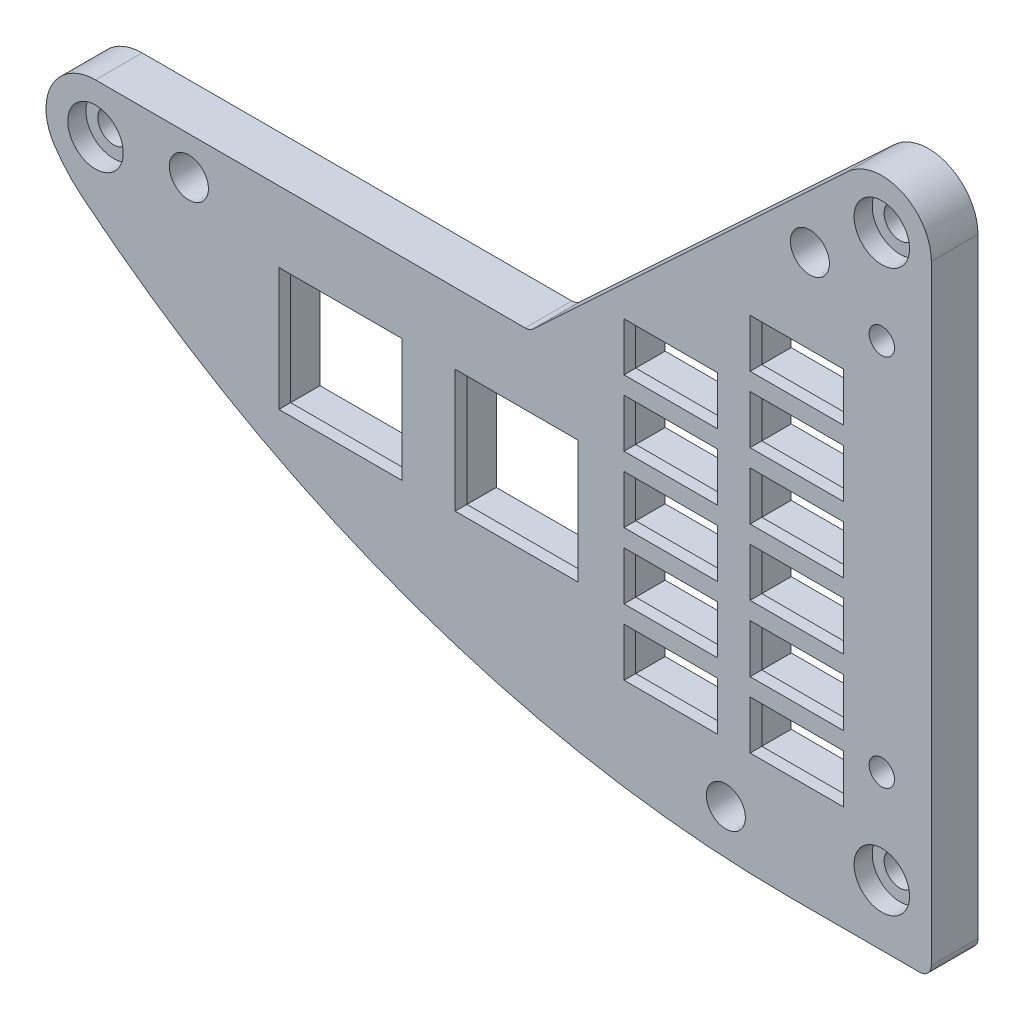
SolidWorks part; units mm, degrees
ref_plane "Front Plane" through (0, 0, 0) normal (0, 0, 1) x (1, 0, 0)
ref_plane "Top Plane" through (0, 0, 0) normal (0, 1, 0) x (1, 0, 0)
ref_plane "Right Plane" through (0, 0, 0) normal (1, 0, 0) x (0, 0, -1)
sketch "Sketch2" plane through (0, 0, -77.851) normal (0, 0, 1) x (1, 0, 0)
  line L0 (-595.8647, 521.6144) -> (-595.8647, 503.8344) construction
  line L1 (-595.8647, 503.8344) -> (-578.0847, 503.8344) construction
  line L2 (-578.0847, 503.8344) -> (-578.0847, 521.6144) construction
  line L3 (-578.0847, 521.6144) -> (-595.8647, 521.6144) construction
  line L4 (-530.5867, 481.6475) -> (-530.5867, 566.1727)
  line L5 (-541.9099, 571.0939) -> (-585.1967, 530.7013)
  line L6 (-585.1967, 530.7013) -> (-644.2517, 530.7013)
  line L7 (-549.6367, 481.6475) -> (-530.5867, 481.6475)
  line L8 (-530.5867, 481.6475) -> (-530.5867, 566.1727)
  line L9 (-541.9099, 571.0939) -> (-585.1967, 530.7013)
  line L10 (-585.1967, 530.7013) -> (-644.2517, 530.7013)
  line L11 (-549.6367, 481.6475) -> (-530.5867, 481.6475)
  line L12 (-572.3697, 495.935) -> (-559.6697, 495.935) construction
  line L13 (-559.6697, 495.935) -> (-559.6697, 502.539) construction
  line L14 (-559.6697, 502.539) -> (-572.3697, 502.539) construction
  line L15 (-572.3697, 502.539) -> (-572.3697, 495.935) construction
  line L16 (-572.3697, 504.9266) -> (-559.6697, 504.9266) construction
  line L17 (-559.6697, 504.9266) -> (-559.6697, 511.5306) construction
  line L18 (-559.6697, 511.5306) -> (-572.3697, 511.5306) construction
  line L19 (-572.3697, 511.5306) -> (-572.3697, 504.9266) construction
  line L20 (-555.2247, 502.539) -> (-555.2247, 495.935) construction
  line L21 (-555.2247, 495.935) -> (-542.5247, 495.935) construction
  line L22 (-542.5247, 495.935) -> (-542.5247, 502.539) construction
  line L23 (-542.5247, 502.539) -> (-555.2247, 502.539) construction
  line L24 (-555.2247, 504.9266) -> (-542.5247, 504.9266) construction
  line L25 (-542.5247, 504.9266) -> (-542.5247, 511.5306) construction
  line L26 (-542.5247, 511.5306) -> (-555.2247, 511.5306) construction
  line L27 (-555.2247, 511.5306) -> (-555.2247, 504.9266) construction
  line L28 (-555.2247, 513.9182) -> (-542.5247, 513.9182) construction
  line L29 (-542.5247, 513.9182) -> (-542.5247, 520.5222) construction
  line L30 (-542.5247, 520.5222) -> (-555.2247, 520.5222) construction
  line L31 (-555.2247, 520.5222) -> (-555.2247, 513.9182) construction
  line L32 (-572.3697, 513.9182) -> (-559.6697, 513.9182) construction
  line L33 (-559.6697, 513.9182) -> (-559.6697, 520.5222) construction
  line L34 (-559.6697, 520.5222) -> (-572.3697, 520.5222) construction
  line L35 (-572.3697, 520.5222) -> (-572.3697, 513.9182) construction
  line L36 (-572.3697, 522.9098) -> (-559.6697, 522.9098) construction
  line L37 (-559.6697, 522.9098) -> (-559.6697, 529.5138) construction
  line L38 (-559.6697, 529.5138) -> (-572.3697, 529.5138) construction
  line L39 (-572.3697, 529.5138) -> (-572.3697, 522.9098) construction
  line L40 (-555.2247, 522.9098) -> (-542.5247, 522.9098) construction
  line L41 (-542.5247, 522.9098) -> (-542.5247, 529.5138) construction
  line L42 (-542.5247, 529.5138) -> (-555.2247, 529.5138) construction
  line L43 (-555.2247, 529.5138) -> (-555.2247, 522.9098) construction
  line L44 (-555.2247, 531.9014) -> (-542.5247, 531.9014) construction
  line L45 (-542.5247, 531.9014) -> (-542.5247, 538.5054) construction
  line L46 (-542.5247, 538.5054) -> (-555.2247, 538.5054) construction
  line L47 (-555.2247, 538.5054) -> (-555.2247, 531.9014) construction
  line L48 (-572.3697, 531.9014) -> (-559.6697, 531.9014) construction
  line L49 (-559.6697, 531.9014) -> (-559.6697, 538.5054) construction
  line L50 (-559.6697, 538.5054) -> (-572.3697, 538.5054) construction
  line L51 (-572.3697, 538.5054) -> (-572.3697, 531.9014) construction
  line L52 (-555.2247, 540.893) -> (-542.5247, 540.893) construction
  line L53 (-542.5247, 540.893) -> (-542.5247, 547.497) construction
  line L54 (-542.5247, 547.497) -> (-555.2247, 547.497) construction
  line L55 (-555.2247, 547.497) -> (-555.2247, 540.893) construction
  line L56 (-555.2247, 513.9182) -> (-542.5247, 513.9182) construction
  line L57 (-595.8647, 521.6144) -> (-595.8647, 503.8344) construction
  line L58 (-595.8647, 503.8344) -> (-578.0847, 503.8344) construction
  line L59 (-578.0847, 503.8344) -> (-578.0847, 521.6144) construction
  line L60 (-578.0847, 521.6144) -> (-595.8647, 521.6144) construction
  line L61 (-572.3697, 495.935) -> (-559.6697, 495.935)
  line L62 (-559.6697, 495.935) -> (-559.6697, 502.539)
  line L63 (-559.6697, 502.539) -> (-572.3697, 502.539)
  line L64 (-572.3697, 502.539) -> (-572.3697, 495.935)
  line L65 (-572.3697, 504.9266) -> (-559.6697, 504.9266)
  line L66 (-559.6697, 504.9266) -> (-559.6697, 511.5306)
  line L67 (-559.6697, 511.5306) -> (-572.3697, 511.5306)
  line L68 (-572.3697, 511.5306) -> (-572.3697, 504.9266)
  line L69 (-555.2247, 502.539) -> (-555.2247, 495.935)
  line L70 (-555.2247, 495.935) -> (-542.5247, 495.935)
  line L71 (-542.5247, 495.935) -> (-542.5247, 502.539)
  line L72 (-542.5247, 502.539) -> (-555.2247, 502.539)
  line L73 (-555.2247, 504.9266) -> (-542.5247, 504.9266)
  line L74 (-542.5247, 504.9266) -> (-542.5247, 511.5306)
  line L75 (-542.5247, 511.5306) -> (-555.2247, 511.5306)
  line L76 (-555.2247, 511.5306) -> (-555.2247, 504.9266)
  line L77 (-555.2247, 513.9182) -> (-542.5247, 513.9182)
  line L78 (-542.5247, 513.9182) -> (-542.5247, 520.5222)
  line L79 (-542.5247, 520.5222) -> (-555.2247, 520.5222)
  line L80 (-555.2247, 520.5222) -> (-555.2247, 513.9182)
  line L81 (-572.3697, 513.9182) -> (-559.6697, 513.9182)
  line L82 (-559.6697, 513.9182) -> (-559.6697, 520.5222)
  line L83 (-559.6697, 520.5222) -> (-572.3697, 520.5222)
  line L84 (-572.3697, 520.5222) -> (-572.3697, 513.9182)
  line L85 (-572.3697, 522.9098) -> (-559.6697, 522.9098)
  line L86 (-559.6697, 522.9098) -> (-559.6697, 529.5138)
  line L87 (-559.6697, 529.5138) -> (-572.3697, 529.5138)
  line L88 (-572.3697, 529.5138) -> (-572.3697, 522.9098)
  line L89 (-555.2247, 522.9098) -> (-542.5247, 522.9098)
  line L90 (-542.5247, 522.9098) -> (-542.5247, 529.5138)
  line L91 (-542.5247, 529.5138) -> (-555.2247, 529.5138)
  line L92 (-555.2247, 529.5138) -> (-555.2247, 522.9098)
  line L93 (-555.2247, 531.9014) -> (-542.5247, 531.9014)
  line L94 (-542.5247, 531.9014) -> (-542.5247, 538.5054)
  line L95 (-542.5247, 538.5054) -> (-555.2247, 538.5054)
  line L96 (-555.2247, 538.5054) -> (-555.2247, 531.9014)
  line L97 (-572.3697, 531.9014) -> (-559.6697, 531.9014)
  line L98 (-559.6697, 531.9014) -> (-559.6697, 538.5054)
  line L99 (-559.6697, 538.5054) -> (-572.3697, 538.5054)
  line L100 (-572.3697, 538.5054) -> (-572.3697, 531.9014)
  line L101 (-555.2247, 540.893) -> (-542.5247, 540.893)
  line L102 (-542.5247, 540.893) -> (-542.5247, 547.497)
  line L103 (-542.5247, 547.497) -> (-555.2247, 547.497)
  line L104 (-555.2247, 547.497) -> (-555.2247, 540.893)
  line L105 (-555.2247, 513.9182) -> (-542.5247, 513.9182)
  line L106 (-578.0847, 503.8344) -> (-595.8647, 521.6144) construction
  line L108 (-578.6181, 521.081) -> (-595.3313, 521.081)
  line L109 (-578.6181, 521.081) -> (-578.6181, 504.3678)
  line L110 (-578.6181, 504.3678) -> (-595.3313, 504.3678)
  line L111 (-595.3313, 521.081) -> (-595.3313, 504.3678)
  line L112 (-578.6181, 521.081) -> (-595.3313, 504.3678) construction
  line L113 (-578.6181, 504.3678) -> (-595.3313, 521.081) construction
  arc A4 (-530.5867, 566.1727) -> (-541.9099, 571.0939) centre (-537.3177, 566.1727) ccw
  arc A5 (-644.2517, 530.7013) -> (-649.8762, 520.2727) centre (-644.2517, 523.9703) ccw
  arc A6 (-649.8762, 520.2727) -> (-646.0191, 515.9958) centre (-634.0129, 530.7013) ccw
  arc A7 (-646.0191, 515.9958) -> (-549.6367, 481.6475) centre (-549.6367, 634.0475) ccw
  arc A8 (-530.5867, 566.1727) -> (-541.9099, 571.0939) centre (-537.3177, 566.1727) ccw
  arc A9 (-644.2517, 530.7013) -> (-649.8762, 520.2727) centre (-644.2517, 523.9703) ccw
  arc A10 (-649.8762, 520.2727) -> (-646.0191, 515.9958) centre (-634.0129, 530.7013) ccw
  arc A11 (-646.0191, 515.9958) -> (-549.6367, 481.6475) centre (-549.6367, 634.0475) ccw
  point P58 (-586.9747, 512.7244)
  dimension "D2" = 16.7132
  dimension "D1" = 0
extrude "Boss-Extrude1" add sketch "Sketch2" against normal blind 6.35 contours A10 A11 L11 L8 A8 L9 L10 A9 L60 L59 L58 L57 L64 L63 L62 L61 L68 L67 L66 L65 L72 L71 L70 L69 L76 L75 L74 L73 L80 L79 L78 L77 L84 L83 L82 L81 L88 L87 L86 L85 L92 L91
hole_wizard "CBORE for #6 Pan Head Machine Screw1" positions "Sketch4" profile "Sketch3" counterbore size "#6" standard "ANSI Inch" end condition through all
sketch "Sketch4" plane through (0, 0, -77.851) normal (0, 0, 1) x (1, 0, 0)
  point P0 (-537.3177, 489.9025)
  point P3 (-537.3177, 566.1727)
  point P6 (-644.2517, 523.9703)
sketch "Sketch3" plane through (-537.3177, 489.9025, -77.851) normal (1, 0, 0) x (0, -1, 0)
  line L0 (0, 0) -> (0, 6.35)
  line L1 (0, 6.35) -> (2.1526, 6.35)
  line L3 (2.1526, 6.35) -> (2.1526, 2.4638)
  line L4 (2.1526, 2.4638) -> (3.7706, 2.4638)
  line L5 (3.7706, 2.4638) -> (3.7706, 0)
  line L7 (3.7706, 0) -> (0, 0)
  line L11 (0, -6.35) -> (0, 107.95) construction
  dimension "Thru Hole Dia." = 4.3053
  dimension "Thru Hole Depth" = 6.35
  dimension "C'Bore Dia." = 7.5413
  dimension "C'Bore Depth" = 2.4638
hole_wizard "#6 Threaded Insert Tapered Hole" positions "Sketch6" profile "Sketch5" legacy
sketch "Sketch6" plane through (0, 0, -77.851) normal (0, 0, 1) x (1, 0, 0)
  point P0 (-558.5267, 487.9975)
  point P3 (-547.0967, 558.9583)
  point P6 (-631.5517, 525.5578)
sketch "Sketch5" plane through (-558.5267, 487.9975, -77.851) normal (1, 0, 0) x (0, -1, 0)
  line L0 (0, 0) -> (0, 3.81)
  line L1 (0, 3.81) -> (2.5273, 3.81)
  line L2 (2.5273, 3.81) -> (2.6543, 0)
  line L3 (2.6543, 0) -> (0, 0)
  line L4 (0, 110) -> (0, -10) construction
  dimension "Minor Diameter" = 5.0546
  dimension "Depth" = 3.81
  dimension "Major Diameter" = 5.3086
sketch "Sketch7" plane through (0, 0, -77.851) normal (0, 0, 1) x (1, 0, 0)
  line L0 (-610.9485, 512.7244) -> (-610.9485, 521.081) construction
  line L2 (-610.9485, 512.7244) -> (-595.3313, 512.7244) construction
  line L3 (-602.5919, 504.3678) -> (-619.3051, 504.3678)
  line L4 (-602.5919, 504.3678) -> (-602.5919, 521.081)
  line L5 (-602.5919, 521.081) -> (-619.3051, 521.081)
  line L6 (-619.3051, 504.3678) -> (-619.3051, 521.081)
  line L7 (-602.5919, 504.3678) -> (-619.3051, 521.081) construction
  line L8 (-602.5919, 521.081) -> (-619.3051, 504.3678) construction
  line L9 (-595.3313, 521.081) -> (-595.3313, 504.3678) construction
  point P5 (-610.9485, 512.7244)
  dimension "D1" = 16.7132
  dimension "D2" = 16.7132
  dimension "D3" = 15.6171
extrude "Cut-Extrude1" cut sketch "Sketch7" against normal through all
sketch "Sketch8" plane through (0, 0, -84.201) normal (0, 0, -1) x (-1, 0, 0)
  line L0 (555.9867, 540.131) -> (555.9867, 548.259)
  line L1 (555.9867, 548.259) -> (541.7627, 548.259)
  line L2 (541.7627, 548.259) -> (541.7627, 540.131)
  line L3 (541.7627, 540.131) -> (555.9867, 540.131)
  line L4 (555.2247, 540.893) -> (555.2247, 547.497)
  line L5 (542.5247, 540.893) -> (555.2247, 540.893)
  line L6 (542.5247, 547.497) -> (542.5247, 540.893)
  line L7 (555.2247, 547.497) -> (542.5247, 547.497)
  line L8 (555.2247, 540.893) -> (555.2247, 547.497) construction
  line L9 (542.5247, 540.893) -> (555.2247, 540.893) construction
  line L10 (542.5247, 547.497) -> (542.5247, 540.893) construction
  line L11 (555.2247, 547.497) -> (542.5247, 547.497) construction
  line L12 (555.2247, 531.9014) -> (555.2247, 538.5054)
  line L13 (542.5247, 531.9014) -> (555.2247, 531.9014)
  line L14 (542.5247, 538.5054) -> (542.5247, 531.9014)
  line L15 (555.2247, 538.5054) -> (542.5247, 538.5054)
  line L16 (555.2247, 531.9014) -> (555.2247, 538.5054) construction
  line L17 (542.5247, 531.9014) -> (555.2247, 531.9014) construction
  line L18 (542.5247, 538.5054) -> (542.5247, 531.9014) construction
  line L19 (555.2247, 538.5054) -> (542.5247, 538.5054) construction
  line L20 (555.2247, 522.9098) -> (555.2247, 529.5138)
  line L21 (542.5247, 522.9098) -> (555.2247, 522.9098)
  line L22 (542.5247, 529.5138) -> (542.5247, 522.9098)
  line L23 (555.2247, 529.5138) -> (542.5247, 529.5138)
  line L24 (555.2247, 522.9098) -> (555.2247, 529.5138) construction
  line L25 (542.5247, 522.9098) -> (555.2247, 522.9098) construction
  line L26 (542.5247, 529.5138) -> (542.5247, 522.9098) construction
  line L27 (555.2247, 529.5138) -> (542.5247, 529.5138) construction
  line L28 (555.2247, 513.9182) -> (555.2247, 520.5222)
  line L29 (542.5247, 513.9182) -> (555.2247, 513.9182)
  line L30 (542.5247, 520.5222) -> (542.5247, 513.9182)
  line L31 (555.2247, 520.5222) -> (542.5247, 520.5222)
  line L32 (555.2247, 513.9182) -> (555.2247, 520.5222) construction
  line L33 (542.5247, 513.9182) -> (555.2247, 513.9182) construction
  line L34 (542.5247, 520.5222) -> (542.5247, 513.9182) construction
  line L35 (555.2247, 520.5222) -> (542.5247, 520.5222) construction
  line L36 (555.2247, 504.9266) -> (555.2247, 511.5306)
  line L37 (542.5247, 504.9266) -> (555.2247, 504.9266)
  line L38 (542.5247, 511.5306) -> (542.5247, 504.9266)
  line L39 (555.2247, 511.5306) -> (542.5247, 511.5306)
  line L40 (555.2247, 504.9266) -> (555.2247, 511.5306) construction
  line L41 (542.5247, 504.9266) -> (555.2247, 504.9266) construction
  line L42 (542.5247, 511.5306) -> (542.5247, 504.9266) construction
  line L43 (555.2247, 511.5306) -> (542.5247, 511.5306) construction
  line L44 (555.2247, 502.539) -> (542.5247, 502.539)
  line L45 (555.2247, 495.935) -> (555.2247, 502.539)
  line L46 (542.5247, 495.935) -> (555.2247, 495.935)
  line L47 (542.5247, 502.539) -> (542.5247, 495.935)
  line L48 (555.2247, 502.539) -> (542.5247, 502.539) construction
  line L49 (555.2247, 495.935) -> (555.2247, 502.539) construction
  line L50 (542.5247, 495.935) -> (555.2247, 495.935) construction
  line L51 (542.5247, 502.539) -> (542.5247, 495.935) construction
  line L52 (572.3697, 531.9014) -> (572.3697, 538.5054)
  line L53 (559.6697, 531.9014) -> (572.3697, 531.9014)
  line L54 (559.6697, 538.5054) -> (559.6697, 531.9014)
  line L55 (572.3697, 538.5054) -> (559.6697, 538.5054)
  line L56 (572.3697, 531.9014) -> (572.3697, 538.5054) construction
  line L57 (559.6697, 531.9014) -> (572.3697, 531.9014) construction
  line L58 (559.6697, 538.5054) -> (559.6697, 531.9014) construction
  line L59 (572.3697, 538.5054) -> (559.6697, 538.5054) construction
  line L60 (572.3697, 522.9098) -> (572.3697, 529.5138)
  line L61 (559.6697, 522.9098) -> (572.3697, 522.9098)
  line L62 (559.6697, 529.5138) -> (559.6697, 522.9098)
  line L63 (572.3697, 529.5138) -> (559.6697, 529.5138)
  line L64 (572.3697, 522.9098) -> (572.3697, 529.5138) construction
  line L65 (559.6697, 522.9098) -> (572.3697, 522.9098) construction
  line L66 (559.6697, 529.5138) -> (559.6697, 522.9098) construction
  line L67 (572.3697, 529.5138) -> (559.6697, 529.5138) construction
  line L68 (572.3697, 513.9182) -> (572.3697, 520.5222)
  line L69 (559.6697, 513.9182) -> (572.3697, 513.9182)
  line L70 (559.6697, 520.5222) -> (559.6697, 513.9182)
  line L71 (572.3697, 520.5222) -> (559.6697, 520.5222)
  line L72 (572.3697, 513.9182) -> (572.3697, 520.5222) construction
  line L73 (559.6697, 513.9182) -> (572.3697, 513.9182) construction
  line L74 (559.6697, 520.5222) -> (559.6697, 513.9182) construction
  line L75 (572.3697, 520.5222) -> (559.6697, 520.5222) construction
  line L76 (572.3697, 504.9266) -> (572.3697, 511.5306)
  line L77 (559.6697, 504.9266) -> (572.3697, 504.9266)
  line L78 (559.6697, 511.5306) -> (559.6697, 504.9266)
  line L79 (572.3697, 511.5306) -> (559.6697, 511.5306)
  line L80 (572.3697, 504.9266) -> (572.3697, 511.5306) construction
  line L81 (559.6697, 504.9266) -> (572.3697, 504.9266) construction
  line L82 (559.6697, 511.5306) -> (559.6697, 504.9266) construction
  line L83 (572.3697, 511.5306) -> (559.6697, 511.5306) construction
  line L84 (572.3697, 495.935) -> (572.3697, 502.539)
  line L85 (559.6697, 495.935) -> (572.3697, 495.935)
  line L86 (559.6697, 502.539) -> (559.6697, 495.935)
  line L87 (572.3697, 502.539) -> (559.6697, 502.539)
  line L88 (572.3697, 495.935) -> (572.3697, 502.539) construction
  line L89 (559.6697, 495.935) -> (572.3697, 495.935) construction
  line L90 (559.6697, 502.539) -> (559.6697, 495.935) construction
  line L91 (572.3697, 502.539) -> (559.6697, 502.539) construction
  line L92 (595.3313, 504.3678) -> (595.3313, 521.081)
  line L93 (578.6181, 504.3678) -> (595.3313, 504.3678)
  line L94 (578.6181, 521.081) -> (578.6181, 504.3678)
  line L95 (595.3313, 521.081) -> (578.6181, 521.081)
  line L96 (595.3313, 504.3678) -> (595.3313, 521.081) construction
  line L97 (578.6181, 504.3678) -> (595.3313, 504.3678) construction
  line L98 (578.6181, 521.081) -> (578.6181, 504.3678) construction
  line L99 (595.3313, 521.081) -> (578.6181, 521.081) construction
  line L100 (555.9867, 531.1394) -> (555.9867, 539.2674)
  line L101 (555.9867, 539.2674) -> (541.7627, 539.2674)
  line L102 (541.7627, 539.2674) -> (541.7627, 531.1394)
  line L103 (541.7627, 531.1394) -> (555.9867, 531.1394)
  line L104 (555.9867, 522.1478) -> (555.9867, 530.2758)
  line L105 (555.9867, 530.2758) -> (541.7627, 530.2758)
  line L106 (541.7627, 530.2758) -> (541.7627, 522.1478)
  line L107 (541.7627, 522.1478) -> (555.9867, 522.1478)
  line L108 (555.9867, 513.1562) -> (555.9867, 521.2842)
  line L109 (555.9867, 521.2842) -> (541.7627, 521.2842)
  line L110 (541.7627, 521.2842) -> (541.7627, 513.1562)
  line L111 (541.7627, 513.1562) -> (555.9867, 513.1562)
  line L112 (555.9867, 504.1646) -> (555.9867, 512.2926)
  line L113 (555.9867, 512.2926) -> (541.7627, 512.2926)
  line L114 (541.7627, 512.2926) -> (541.7627, 504.1646)
  line L115 (541.7627, 504.1646) -> (555.9867, 504.1646)
  line L116 (555.9867, 503.301) -> (541.7627, 503.301)
  line L117 (541.7627, 503.301) -> (541.7627, 495.173)
  line L118 (541.7627, 495.173) -> (555.9867, 495.173)
  line L119 (555.9867, 495.173) -> (555.9867, 503.301)
  line L120 (573.1317, 531.1394) -> (573.1317, 539.2674)
  line L121 (573.1317, 539.2674) -> (558.9077, 539.2674)
  line L122 (558.9077, 539.2674) -> (558.9077, 531.1394)
  line L123 (558.9077, 531.1394) -> (573.1317, 531.1394)
  line L124 (573.1317, 522.1478) -> (573.1317, 530.2758)
  line L125 (573.1317, 530.2758) -> (558.9077, 530.2758)
  line L126 (558.9077, 530.2758) -> (558.9077, 522.1478)
  line L127 (558.9077, 522.1478) -> (573.1317, 522.1478)
  line L128 (573.1317, 513.1562) -> (573.1317, 521.2842)
  line L129 (573.1317, 521.2842) -> (558.9077, 521.2842)
  line L130 (558.9077, 521.2842) -> (558.9077, 513.1562)
  line L131 (558.9077, 513.1562) -> (573.1317, 513.1562)
  line L132 (573.1317, 504.1646) -> (573.1317, 512.2926)
  line L133 (573.1317, 512.2926) -> (558.9077, 512.2926)
  line L134 (558.9077, 512.2926) -> (558.9077, 504.1646)
  line L135 (558.9077, 504.1646) -> (573.1317, 504.1646)
  line L136 (573.1317, 495.173) -> (573.1317, 503.301)
  line L137 (573.1317, 503.301) -> (558.9077, 503.301)
  line L138 (558.9077, 503.301) -> (558.9077, 495.173)
  line L139 (558.9077, 495.173) -> (573.1317, 495.173)
  line L140 (596.0933, 503.6058) -> (596.0933, 521.843)
  line L141 (596.0933, 521.843) -> (577.8561, 521.843)
  line L142 (577.8561, 521.843) -> (577.8561, 503.6058)
  line L143 (577.8561, 503.6058) -> (596.0933, 503.6058)
  line L144 (620.0671, 521.843) -> (601.8299, 521.843)
  line L145 (601.8299, 521.843) -> (601.8299, 503.6058)
  line L146 (601.8299, 503.6058) -> (620.0671, 503.6058)
  line L147 (620.0671, 503.6058) -> (620.0671, 521.843)
  line L148 (619.3051, 521.081) -> (602.5919, 521.081)
  line L149 (619.3051, 504.3678) -> (619.3051, 521.081)
  line L150 (602.5919, 504.3678) -> (619.3051, 504.3678)
  line L151 (602.5919, 521.081) -> (602.5919, 504.3678)
  line L152 (619.3051, 521.081) -> (602.5919, 521.081) construction
  line L153 (619.3051, 504.3678) -> (619.3051, 521.081) construction
  line L154 (602.5919, 504.3678) -> (619.3051, 504.3678) construction
  line L155 (602.5919, 521.081) -> (602.5919, 504.3678) construction
  dimension "D1" = 0
  dimension "D2" = 0
  dimension "D3" = 0
  dimension "D4" = 0
  dimension "D5" = 0
  dimension "D6" = 0
  dimension "D7" = 0
  dimension "D8" = 0
  dimension "D9" = 0
  dimension "D10" = 0
  dimension "D11" = 0
  dimension "D12" = 0
  dimension "D13" = 0.762
  dimension "D14" = 0
  dimension "D15" = 0.762
extrude "Cut-Extrude2" cut sketch "Sketch8" against normal offset from surface (4.7625 mm away) 1.5875 up to face at (-610.9485, 512.7244, -77.851)
fillet "Fillet1" radius 1.5875 2 edges at (-585.1967, 530.7013, -81.026) (-530.5867, 481.6475, -81.026)
hole_wizard "#4 Clearance Hole1" positions "Sketch10" profile "Sketch9" hole size "#4" standard "ANSI Inch" end condition through all
sketch "Sketch10" plane through (0, 0, -77.851) normal (0, 0, 1) x (1, 0, 0)
  point P0 (-537.3177, 502.6376)
  point P3 (-537.3177, 553.4376)
sketch "Sketch9" plane through (-537.3177, 502.6376, -77.851) normal (1, 0, 0) x (0, -1, 0)
  line L0 (0, 0) -> (0, 6.35)
  line L1 (0, 6.35) -> (1.7272, 6.35)
  line L2 (1.7272, 6.35) -> (1.7272, 0)
  line L5 (1.7272, 0) -> (0, 0)
  line L11 (0, -6.35) -> (0, 107.95) construction
  dimension "Thru Hole Dia." = 3.4544
  dimension "Thru Hole Depth" = 6.35
hole_wizard "Hole2" positions "Sketch12" profile "Sketch11" legacy
sketch "Sketch12" plane through (0, 0, -84.201) normal (0, 0, -1) x (-1, 0, 0)
  point P0 (642.6555, 517.9926)
sketch "Sketch11" plane through (-642.6555, 517.9926, -84.201) normal (1, 0, 0) x (0, 1, 0)
  line L0 (0, 0) -> (0, 3.429)
  line L1 (0, 3.429) -> (1.9431, 3.429)
  line L2 (1.9431, 3.429) -> (2.0701, 0)
  line L3 (2.0701, 0) -> (0, 0)
  line L4 (0, 110) -> (0, -10) construction
  dimension "Minor Diameter" = 3.8862
  dimension "Depth" = 3.429
  dimension "Major Diameter" = 4.1402
hole_wizard "#4 Clearance Hole2" positions "Sketch14" profile "Sketch13" hole size "#4" standard "ANSI Inch"
sketch "Sketch14" plane through (0, 0, -80.772) normal (0, 0, -1) x (-1, 0, 0)
  point P2 (642.6555, 517.9926)
sketch "Sketch13" plane through (-642.6555, 517.9926, -80.772) normal (1, 0, 0) x (0, 1, 0)
  line L0 (0, 0) -> (0, 1.5875)
  line L1 (0, 1.5875) -> (1.7272, 1.5875)
  line L2 (1.7272, 1.5875) -> (1.7272, 0)
  line L5 (1.7272, 0) -> (0, 0)
  line L10 (0, 1.5875) -> (-1.7272, 1.5875) construction
  line L11 (0, -6.35) -> (0, 107.95) construction
  dimension "Hole Dia." = 3.4544
  dimension "Hole Depth" = 1.5875
  dimension "Drill Angle" = 180
hole_wizard "#6 Clearance Hole1" positions "Sketch16" profile "Sketch15" hole size "#6" standard "ANSI Inch" end condition through all
sketch "Sketch16" plane through (0, 0, -81.661) normal (0, 0, 1) x (1, 0, 0)
  point P0 (-558.5267, 487.9975)
  point P3 (-631.5517, 525.5578)
  point P6 (-547.0967, 558.9583)
sketch "Sketch15" plane through (-558.5267, 487.9975, -81.661) normal (1, 0, 0) x (0, -1, 0)
  line L0 (0, 0) -> (0, 2.54)
  line L1 (0, 2.54) -> (2.1526, 2.54)
  line L2 (2.1526, 2.54) -> (2.1526, 0)
  line L5 (2.1526, 0) -> (0, 0)
  line L11 (0, -6.35) -> (0, 107.95) construction
  dimension "Thru Hole Dia." = 4.3053
  dimension "Thru Hole Depth" = 2.54
equation "\"D2@Sketch7\"=\"D1@Sketch7\""
